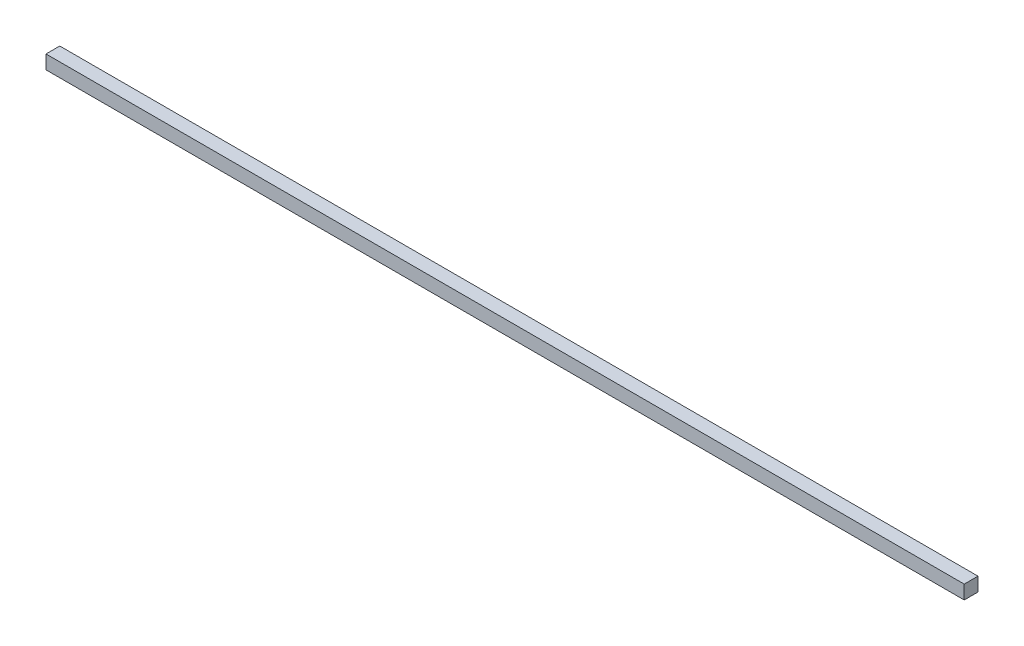
SolidWorks part; units mm, degrees
ref_plane "Plan de face" through (0, 0, 0) normal (0, 0, 1) x (1, 0, 0)
ref_plane "Plan de dessus" through (0, 0, 0) normal (0, 1, 0) x (1, 0, 0)
ref_plane "Plan de droite" through (0, 0, 0) normal (1, 0, 0) x (0, 0, -1)
sketch "Esquisse1" plane through (0, 0, 0) normal (0, 0, 1) x (1, 0, 0)
  line L0 (-113.8134, -33.4903) -> (-113.8134, -36.4903)
  line L1 (-113.8134, -33.4903) -> (86.1866, -33.4903)
  line L2 (-113.8134, -36.4903) -> (86.1866, -36.4903)
  line L3 (86.1866, -33.4903) -> (86.1866, -36.4903)
  dimension "D1" = 200
  dimension "D2" = 3
extrude "Boss.-Extru.1" add sketch "Esquisse1" along normal blind 3
